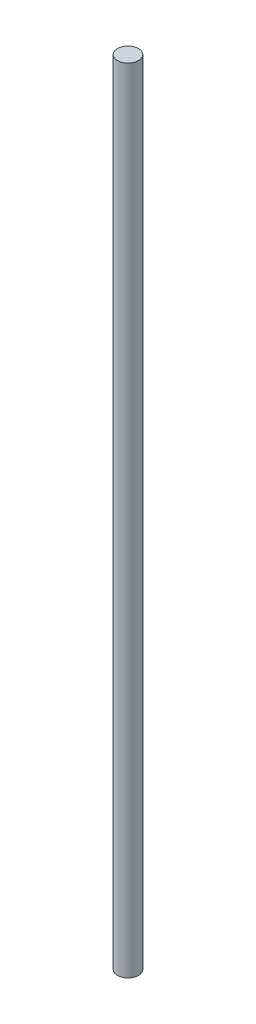
SolidWorks part; units mm, degrees
ref_plane "Alzado" through (0, 0, 0) normal (0, 0, 1) x (1, 0, 0)
ref_plane "Planta" through (0, 0, 0) normal (0, 1, 0) x (1, 0, 0)
ref_plane "Vista lateral" through (0, 0, 0) normal (1, 0, 0) x (0, 0, -1)
sketch "Croquis1" plane through (0, 0, 0) normal (0, 1, 0) x (1, 0, 0)
  circle A0 centre (0, 0) radius 6.35
  dimension "D1" = 12.7
sketch "Croquis2" plane through (0, 0, 0) normal (0, 0, 1) x (1, 0, 0)
  line L0 (0, 0) -> (0, 480)
  dimension "D1" = 480
sweep "Barrer1" add profiles "Croquis1" path "Croquis2"
